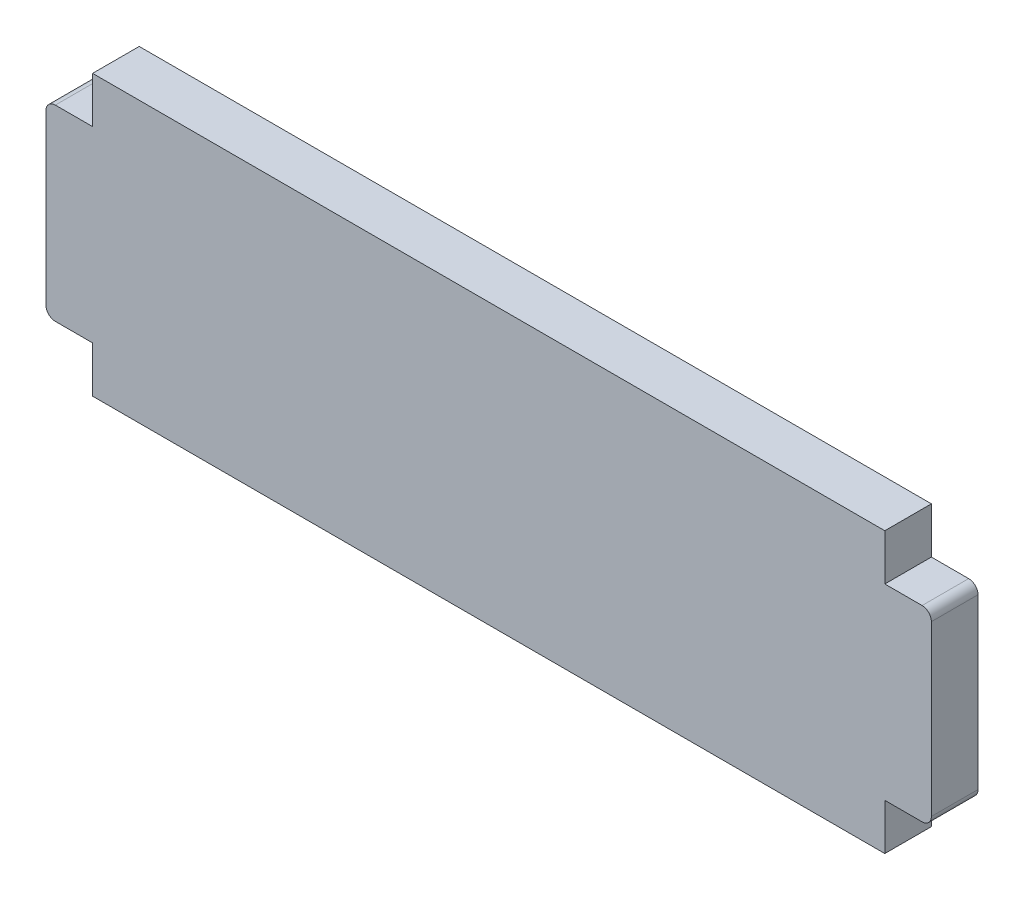
SolidWorks part; units mm, degrees
ref_plane "Front" through (0, 0, 0) normal (0, 0, 1) x (1, 0, 0)
ref_plane "Top" through (0, 0, 0) normal (0, 1, 0) x (1, 0, 0)
ref_plane "Right" through (0, 0, 0) normal (1, 0, 0) x (0, 0, -1)
sketch "Sketch1" plane through (0, 0, 0) normal (0, 0, 1) x (1, 0, 0)
  line L0 (85, 25.05) -> (85, 30)
  line L1 (0, 0) -> (85, 0)
  line L2 (0, 0) -> (0, 4.95)
  line L3 (0, 30) -> (85, 30)
  line L4 (85, 0) -> (85, 4.95)
  line L5 (0, 25.05) -> (-5, 25.05)
  line L7 (0, 4.95) -> (-5, 4.95)
  line L8 (-5, 25.05) -> (-5, 4.95)
  line L9 (85, 25.05) -> (90, 25.05)
  line L11 (85, 4.95) -> (90, 4.95)
  line L12 (90, 25.05) -> (90, 4.95)
  line L13 (0, 25.05) -> (0, 30)
  dimension "D1" = 85
  dimension "D2" = 30
  dimension "D3" = 5
  dimension "D4" = 4.95
  dimension "D5" = 20.1
  dimension "D6" = 4.95
  dimension "D7" = 5
  dimension "D8" = 20.1
extrude "Boss-Extrude1" add sketch "Sketch1" along normal blind 5
fillet "Fillet1" radius 1 4 edges at (-5, 4.95, 2.5) (-5, 25.05, 2.5) (90, 4.95, 2.5) (90, 25.05, 2.5)
